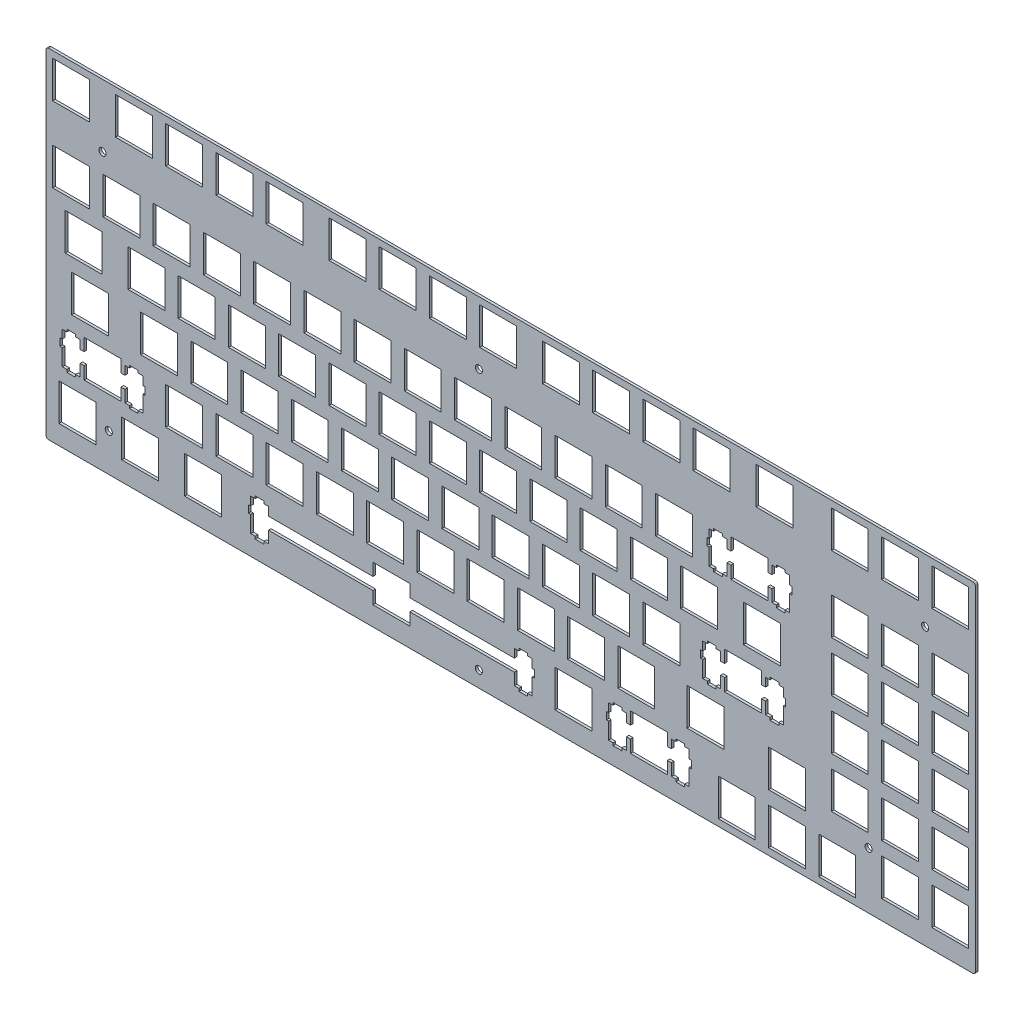
SolidWorks part; units mm, degrees
ref_plane "前视基准面" through (0, 0, 0) normal (0, 0, 1) x (1, 0, 0)
ref_plane "上视基准面" through (0, 0, 0) normal (0, 1, 0) x (1, 0, 0)
ref_plane "右视基准面" through (0, 0, 0) normal (1, 0, 0) x (0, 0, -1)
other "Configuration Table"
sketch "Model" plane through (0, 0, 0) normal (0, 0, 1) x (1, 0, 0)
  line L0 (0.0951, 129.021) -> (352.52, 129.021)
  line L1 (352.52, 129.021) -> (352.52, 0.4341)
  line L2 (352.52, 0.4341) -> (0.0951, 0.4341)
  line L3 (0.0951, 0.4341) -> (0.0951, 129.021)
  line L4 (255.032, 16.9595) -> (269.032, 16.9595)
  line L5 (269.032, 16.9595) -> (269.032, 2.96)
  line L6 (269.032, 2.96) -> (255.032, 2.96)
  line L7 (255.032, 2.96) -> (255.032, 16.9595)
  line L8 (274.082, 16.9595) -> (288.082, 16.9595)
  line L9 (288.082, 16.9595) -> (288.082, 2.96)
  line L10 (288.082, 2.96) -> (274.082, 2.96)
  line L11 (274.082, 2.96) -> (274.082, 16.9595)
  line L12 (293.132, 16.9595) -> (307.132, 16.9595)
  line L13 (307.132, 16.9595) -> (307.132, 2.96)
  line L14 (307.132, 2.96) -> (293.132, 2.96)
  line L15 (293.132, 2.96) -> (293.132, 16.9595)
  line L16 (124.062, 21.722) -> (124.062, 17.0215)
  line L17 (124.062, 17.0215) -> (84.4381, 17.0215)
  line L18 (84.4381, 17.0215) -> (84.4381, 20.2517)
  line L19 (84.4381, 20.2517) -> (82.7126, 20.2517)
  line L20 (82.7126, 20.2517) -> (82.7126, 21.1722)
  line L21 (82.7126, 21.1722) -> (79.412, 21.1722)
  line L22 (79.412, 21.1722) -> (79.412, 20.2517)
  line L23 (79.412, 20.2517) -> (77.687, 20.2517)
  line L24 (77.687, 20.2517) -> (77.687, 17.0215)
  line L25 (77.687, 17.0215) -> (76.8629, 17.0215)
  line L26 (76.8629, 17.0215) -> (76.8629, 14.2227)
  line L27 (76.8629, 14.2227) -> (77.687, 14.2227)
  line L28 (77.687, 14.2227) -> (77.687, 7.9527)
  line L29 (77.687, 7.9527) -> (79.412, 7.9527)
  line L30 (79.412, 7.9527) -> (79.412, 6.9715)
  line L31 (79.412, 6.9715) -> (82.7126, 6.9715)
  line L32 (82.7126, 6.9715) -> (82.7126, 7.9527)
  line L33 (82.7126, 7.9527) -> (84.4381, 7.9527)
  line L34 (84.4381, 7.9527) -> (84.4381, 12.4216)
  line L35 (84.4381, 12.4216) -> (124.062, 12.4216)
  line L36 (124.062, 12.4216) -> (124.062, 7.7225)
  line L37 (124.062, 7.7225) -> (138.063, 7.7225)
  line L38 (138.063, 7.7225) -> (138.063, 12.4216)
  line L39 (138.063, 12.4216) -> (177.687, 12.4216)
  line L40 (177.687, 12.4216) -> (177.687, 7.9527)
  line L41 (177.687, 7.9527) -> (179.412, 7.9527)
  line L42 (179.412, 7.9527) -> (179.412, 6.9715)
  line L43 (179.412, 6.9715) -> (182.713, 6.9715)
  line L44 (182.713, 6.9715) -> (182.713, 7.9527)
  line L45 (182.713, 7.9527) -> (184.438, 7.9527)
  line L46 (184.438, 7.9527) -> (184.438, 14.2227)
  line L47 (184.438, 14.2227) -> (185.262, 14.2227)
  line L48 (185.262, 14.2227) -> (185.262, 17.0215)
  line L49 (185.262, 17.0215) -> (184.438, 17.0215)
  line L50 (184.438, 17.0215) -> (184.438, 20.2517)
  line L51 (184.438, 20.2517) -> (182.713, 20.2517)
  line L52 (182.713, 20.2517) -> (182.713, 21.1722)
  line L53 (182.713, 21.1722) -> (179.412, 21.1722)
  line L54 (179.412, 21.1722) -> (179.412, 20.2517)
  line L55 (179.412, 20.2517) -> (177.687, 20.2517)
  line L56 (177.687, 20.2517) -> (177.687, 17.0215)
  line L57 (177.687, 17.0215) -> (138.063, 17.0215)
  line L58 (138.063, 17.0215) -> (138.063, 21.722)
  line L59 (138.063, 21.722) -> (124.062, 21.722)
  line L60 (221.695, 21.722) -> (221.695, 17.0215)
  line L61 (221.695, 17.0215) -> (220.169, 17.0215)
  line L62 (220.169, 17.0215) -> (220.169, 20.2517)
  line L63 (220.169, 20.2517) -> (218.444, 20.2517)
  line L64 (218.444, 20.2517) -> (218.444, 21.1722)
  line L65 (218.444, 21.1722) -> (215.145, 21.1722)
  line L66 (215.145, 21.1722) -> (215.145, 20.2517)
  line L67 (215.145, 20.2517) -> (213.42, 20.2517)
  line L68 (213.42, 20.2517) -> (213.42, 17.0215)
  line L69 (213.42, 17.0215) -> (212.594, 17.0215)
  line L70 (212.594, 17.0215) -> (212.594, 14.2227)
  line L71 (212.594, 14.2227) -> (213.42, 14.2227)
  line L72 (213.42, 14.2227) -> (213.42, 7.9527)
  line L73 (213.42, 7.9527) -> (215.145, 7.9527)
  line L74 (215.145, 7.9527) -> (215.145, 6.9715)
  line L75 (215.145, 6.9715) -> (218.444, 6.9715)
  line L76 (218.444, 6.9715) -> (218.444, 7.9527)
  line L77 (218.444, 7.9527) -> (220.169, 7.9527)
  line L78 (220.169, 7.9527) -> (220.169, 12.4216)
  line L79 (220.169, 12.4216) -> (221.695, 12.4216)
  line L80 (221.695, 12.4216) -> (221.695, 7.7225)
  line L81 (221.695, 7.7225) -> (235.694, 7.7225)
  line L82 (235.694, 7.7225) -> (235.694, 12.4216)
  line L83 (235.694, 12.4216) -> (237.22, 12.4216)
  line L84 (237.22, 12.4216) -> (237.22, 7.9527)
  line L85 (237.22, 7.9527) -> (238.945, 7.9527)
  line L86 (238.945, 7.9527) -> (238.945, 6.9715)
  line L87 (238.945, 6.9715) -> (242.244, 6.9715)
  line L88 (242.244, 6.9715) -> (242.244, 7.9527)
  line L89 (242.244, 7.9527) -> (243.969, 7.9527)
  line L90 (243.969, 7.9527) -> (243.969, 14.2227)
  line L91 (243.969, 14.2227) -> (244.795, 14.2227)
  line L92 (244.795, 14.2227) -> (244.795, 17.0215)
  line L93 (244.795, 17.0215) -> (243.969, 17.0215)
  line L94 (243.969, 17.0215) -> (243.969, 20.2517)
  line L95 (243.969, 20.2517) -> (242.244, 20.2517)
  line L96 (242.244, 20.2517) -> (242.244, 21.1722)
  line L97 (242.244, 21.1722) -> (238.945, 21.1722)
  line L98 (238.945, 21.1722) -> (238.945, 20.2517)
  line L99 (238.945, 20.2517) -> (237.22, 20.2517)
  line L100 (237.22, 20.2517) -> (237.22, 17.0215)
  line L101 (237.22, 17.0215) -> (235.694, 17.0215)
  line L102 (235.694, 17.0215) -> (235.694, 21.722)
  line L103 (235.694, 21.722) -> (221.695, 21.722)
  line L104 (5.0009, 21.722) -> (19.0004, 21.722)
  line L105 (19.0004, 21.722) -> (19.0004, 7.7225)
  line L106 (19.0004, 7.7225) -> (5.0009, 7.7225)
  line L107 (5.0009, 7.7225) -> (5.0009, 21.722)
  line L108 (28.812, 21.722) -> (42.8128, 21.722)
  line L109 (42.8128, 21.722) -> (42.8128, 7.7225)
  line L110 (42.8128, 7.7225) -> (28.812, 7.7225)
  line L111 (28.812, 7.7225) -> (28.812, 21.722)
  line L112 (52.626, 21.722) -> (66.6253, 21.722)
  line L113 (66.6253, 21.722) -> (66.6253, 7.7225)
  line L114 (66.6253, 7.7225) -> (52.626, 7.7225)
  line L115 (52.626, 7.7225) -> (52.626, 21.722)
  line L116 (193.12, 21.722) -> (207.119, 21.722)
  line L117 (207.119, 21.722) -> (207.119, 7.7225)
  line L118 (207.119, 7.7225) -> (193.12, 7.7225)
  line L119 (193.12, 7.7225) -> (193.12, 21.722)
  line L120 (316.945, 21.722) -> (330.944, 21.722)
  line L121 (330.944, 21.722) -> (330.944, 7.7225)
  line L122 (330.944, 7.7225) -> (316.945, 7.7225)
  line L123 (316.945, 7.7225) -> (316.945, 21.722)
  line L124 (335.995, 21.722) -> (349.994, 21.722)
  line L125 (349.994, 21.722) -> (349.994, 7.7225)
  line L126 (349.994, 7.7225) -> (335.995, 7.7225)
  line L127 (335.995, 7.7225) -> (335.995, 21.722)
  line L128 (274.082, 36.0094) -> (288.082, 36.0094)
  line L129 (288.082, 36.0094) -> (288.082, 22.01)
  line L130 (288.082, 22.01) -> (274.082, 22.01)
  line L131 (274.082, 22.01) -> (274.082, 36.0094)
  line L132 (14.5259, 40.7719) -> (14.5259, 36.0715)
  line L133 (14.5259, 36.0715) -> (13.0004, 36.0715)
  line L134 (13.0004, 36.0715) -> (13.0004, 39.3016)
  line L135 (13.0004, 39.3016) -> (11.2751, 39.3016)
  line L136 (11.2751, 39.3016) -> (11.2751, 40.2223)
  line L137 (11.2751, 40.2223) -> (7.9761, 40.2223)
  line L138 (7.9761, 40.2223) -> (7.9761, 39.3016)
  line L139 (7.9761, 39.3016) -> (6.2508, 39.3016)
  line L140 (6.2508, 39.3016) -> (6.2508, 36.0715)
  line L141 (6.2508, 36.0715) -> (5.4253, 36.0715)
  line L142 (5.4253, 36.0715) -> (5.4253, 33.2727)
  line L143 (5.4253, 33.2727) -> (6.2508, 33.2727)
  line L144 (6.2508, 33.2727) -> (6.2508, 27.0027)
  line L145 (6.2508, 27.0027) -> (7.9761, 27.0027)
  line L146 (7.9761, 27.0027) -> (7.9761, 26.0215)
  line L147 (7.9761, 26.0215) -> (11.2751, 26.0215)
  line L148 (11.2751, 26.0215) -> (11.2751, 27.0027)
  line L149 (11.2751, 27.0027) -> (13.0004, 27.0027)
  line L150 (13.0004, 27.0027) -> (13.0004, 31.4716)
  line L151 (13.0004, 31.4716) -> (14.5259, 31.4716)
  line L152 (14.5259, 31.4716) -> (14.5259, 26.7725)
  line L153 (14.5259, 26.7725) -> (28.5254, 26.7725)
  line L154 (28.5254, 26.7725) -> (28.5254, 31.4716)
  line L155 (28.5254, 31.4716) -> (30.0509, 31.4716)
  line L156 (30.0509, 31.4716) -> (30.0509, 27.0027)
  line L157 (30.0509, 27.0027) -> (31.7748, 27.0027)
  line L158 (31.7748, 27.0027) -> (31.7748, 26.0215)
  line L159 (31.7748, 26.0215) -> (35.0752, 26.0215)
  line L160 (35.0752, 26.0215) -> (35.0752, 27.0027)
  line L161 (35.0752, 27.0027) -> (36.8004, 27.0027)
  line L162 (36.8004, 27.0027) -> (36.8004, 33.2727)
  line L163 (36.8004, 33.2727) -> (37.6259, 33.2727)
  line L164 (37.6259, 33.2727) -> (37.6259, 36.0715)
  line L165 (37.6259, 36.0715) -> (36.8004, 36.0715)
  line L166 (36.8004, 36.0715) -> (36.8004, 39.3016)
  line L167 (36.8004, 39.3016) -> (35.0752, 39.3016)
  line L168 (35.0752, 39.3016) -> (35.0752, 40.2223)
  line L169 (35.0752, 40.2223) -> (31.7748, 40.2223)
  line L170 (31.7748, 40.2223) -> (31.7748, 39.3016)
  line L171 (31.7748, 39.3016) -> (30.0509, 39.3016)
  line L172 (30.0509, 39.3016) -> (30.0509, 36.0715)
  line L173 (30.0509, 36.0715) -> (28.5254, 36.0715)
  line L174 (28.5254, 36.0715) -> (28.5254, 40.7719)
  line L175 (28.5254, 40.7719) -> (14.5259, 40.7719)
  line L176 (45.4822, 40.7719) -> (59.4815, 40.7719)
  line L177 (59.4815, 40.7719) -> (59.4815, 26.7725)
  line L178 (59.4815, 26.7725) -> (45.4822, 26.7725)
  line L179 (45.4822, 26.7725) -> (45.4822, 40.7719)
  line L180 (64.5322, 40.7719) -> (78.5315, 40.7719)
  line L181 (78.5315, 40.7719) -> (78.5315, 26.7725)
  line L182 (78.5315, 26.7725) -> (64.5322, 26.7725)
  line L183 (64.5322, 26.7725) -> (64.5322, 40.7719)
  line L184 (83.5822, 40.7719) -> (97.5815, 40.7719)
  line L185 (97.5815, 40.7719) -> (97.5815, 26.7725)
  line L186 (97.5815, 26.7725) -> (83.5822, 26.7725)
  line L187 (83.5822, 26.7725) -> (83.5822, 40.7719)
  line L188 (102.632, 40.7719) -> (116.632, 40.7719)
  line L189 (116.632, 40.7719) -> (116.632, 26.7725)
  line L190 (116.632, 26.7725) -> (102.632, 26.7725)
  line L191 (102.632, 26.7725) -> (102.632, 40.7719)
  line L192 (121.682, 40.7719) -> (135.682, 40.7719)
  line L193 (135.682, 40.7719) -> (135.682, 26.7725)
  line L194 (135.682, 26.7725) -> (121.682, 26.7725)
  line L195 (121.682, 26.7725) -> (121.682, 40.7719)
  line L196 (140.732, 40.7719) -> (154.732, 40.7719)
  line L197 (154.732, 40.7719) -> (154.732, 26.7725)
  line L198 (154.732, 26.7725) -> (140.732, 26.7725)
  line L199 (140.732, 26.7725) -> (140.732, 40.7719)
  line L200 (159.782, 40.7719) -> (173.782, 40.7719)
  line L201 (173.782, 40.7719) -> (173.782, 26.7725)
  line L202 (173.782, 26.7725) -> (159.782, 26.7725)
  line L203 (159.782, 26.7725) -> (159.782, 40.7719)
  line L204 (178.832, 40.7719) -> (192.832, 40.7719)
  line L205 (192.832, 40.7719) -> (192.832, 26.7725)
  line L206 (192.832, 26.7725) -> (178.832, 26.7725)
  line L207 (178.832, 26.7725) -> (178.832, 40.7719)
  line L208 (197.882, 40.7719) -> (211.882, 40.7719)
  line L209 (211.882, 40.7719) -> (211.882, 26.7725)
  line L210 (211.882, 26.7725) -> (197.882, 26.7725)
  line L211 (197.882, 26.7725) -> (197.882, 40.7719)
  line L212 (216.932, 40.7719) -> (230.932, 40.7719)
  line L213 (230.932, 40.7719) -> (230.932, 26.7725)
  line L214 (230.932, 26.7725) -> (216.932, 26.7725)
  line L215 (216.932, 26.7725) -> (216.932, 40.7719)
  line L216 (243.126, 40.7719) -> (257.125, 40.7719)
  line L217 (257.125, 40.7719) -> (257.125, 26.7725)
  line L218 (257.125, 26.7725) -> (243.126, 26.7725)
  line L219 (243.126, 26.7725) -> (243.126, 40.7719)
  line L220 (297.895, 40.7719) -> (311.894, 40.7719)
  line L221 (311.894, 40.7719) -> (311.894, 26.7725)
  line L222 (311.894, 26.7725) -> (297.895, 26.7725)
  line L223 (297.895, 26.7725) -> (297.895, 40.7719)
  line L224 (316.945, 40.7719) -> (330.944, 40.7719)
  line L225 (330.944, 40.7719) -> (330.944, 26.7725)
  line L226 (330.944, 26.7725) -> (316.945, 26.7725)
  line L227 (316.945, 26.7725) -> (316.945, 40.7719)
  line L228 (335.995, 40.7719) -> (349.994, 40.7719)
  line L229 (349.994, 40.7719) -> (349.994, 26.7725)
  line L230 (349.994, 26.7725) -> (335.995, 26.7725)
  line L231 (335.995, 26.7725) -> (335.995, 40.7719)
  line L232 (257.412, 59.8219) -> (257.412, 55.1215)
  line L233 (257.412, 55.1215) -> (255.888, 55.1215)
  line L234 (255.888, 55.1215) -> (255.888, 58.3516)
  line L235 (255.888, 58.3516) -> (254.161, 58.3516)
  line L236 (254.161, 58.3516) -> (254.161, 59.2723)
  line L237 (254.161, 59.2723) -> (250.862, 59.2723)
  line L238 (250.862, 59.2723) -> (250.862, 58.3516)
  line L239 (250.862, 58.3516) -> (249.137, 58.3516)
  line L240 (249.137, 58.3516) -> (249.137, 55.1215)
  line L241 (249.137, 55.1215) -> (248.313, 55.1215)
  line L242 (248.313, 55.1215) -> (248.313, 52.3226)
  line L243 (248.313, 52.3226) -> (249.137, 52.3226)
  line L244 (249.137, 52.3226) -> (249.137, 46.0527)
  line L245 (249.137, 46.0527) -> (250.862, 46.0527)
  line L246 (250.862, 46.0527) -> (250.862, 45.0716)
  line L247 (250.862, 45.0716) -> (254.161, 45.0716)
  line L248 (254.161, 45.0716) -> (254.161, 46.0527)
  line L249 (254.161, 46.0527) -> (255.888, 46.0527)
  line L250 (255.888, 46.0527) -> (255.888, 50.5217)
  line L251 (255.888, 50.5217) -> (257.412, 50.5217)
  line L252 (257.412, 50.5217) -> (257.412, 45.8227)
  line L253 (257.412, 45.8227) -> (271.413, 45.8227)
  line L254 (271.413, 45.8227) -> (271.413, 50.5217)
  line L255 (271.413, 50.5217) -> (272.937, 50.5217)
  line L256 (272.937, 50.5217) -> (272.937, 46.0527)
  line L257 (272.937, 46.0527) -> (274.662, 46.0527)
  line L258 (274.662, 46.0527) -> (274.662, 45.0716)
  line L259 (274.662, 45.0716) -> (277.963, 45.0716)
  line L260 (277.963, 45.0716) -> (277.963, 46.0527)
  line L261 (277.963, 46.0527) -> (279.688, 46.0527)
  line L262 (279.688, 46.0527) -> (279.688, 52.3226)
  line L263 (279.688, 52.3226) -> (280.512, 52.3226)
  line L264 (280.512, 52.3226) -> (280.512, 55.1215)
  line L265 (280.512, 55.1215) -> (279.688, 55.1215)
  line L266 (279.688, 55.1215) -> (279.688, 58.3516)
  line L267 (279.688, 58.3516) -> (277.963, 58.3516)
  line L268 (277.963, 58.3516) -> (277.963, 59.2723)
  line L269 (277.963, 59.2723) -> (274.662, 59.2723)
  line L270 (274.662, 59.2723) -> (274.662, 58.3516)
  line L271 (274.662, 58.3516) -> (272.937, 58.3516)
  line L272 (272.937, 58.3516) -> (272.937, 55.1215)
  line L273 (272.937, 55.1215) -> (271.413, 55.1215)
  line L274 (271.413, 55.1215) -> (271.413, 59.8219)
  line L275 (271.413, 59.8219) -> (257.412, 59.8219)
  line L276 (9.762, 59.8219) -> (23.7629, 59.8219)
  line L277 (23.7629, 59.8219) -> (23.7629, 45.8227)
  line L278 (23.7629, 45.8227) -> (9.762, 45.8227)
  line L279 (9.762, 45.8227) -> (9.762, 59.8219)
  line L280 (35.9572, 59.8219) -> (49.9565, 59.8219)
  line L281 (49.9565, 59.8219) -> (49.9565, 45.8227)
  line L282 (49.9565, 45.8227) -> (35.9572, 45.8227)
  line L283 (35.9572, 45.8227) -> (35.9572, 59.8219)
  line L284 (55.0072, 59.8219) -> (69.0065, 59.8219)
  line L285 (69.0065, 59.8219) -> (69.0065, 45.8227)
  line L286 (69.0065, 45.8227) -> (55.0072, 45.8227)
  line L287 (55.0072, 45.8227) -> (55.0072, 59.8219)
  line L288 (74.0572, 59.8219) -> (88.0565, 59.8219)
  line L289 (88.0565, 59.8219) -> (88.0565, 45.8227)
  line L290 (88.0565, 45.8227) -> (74.0572, 45.8227)
  line L291 (74.0572, 45.8227) -> (74.0572, 59.8219)
  line L292 (93.1072, 59.8219) -> (107.107, 59.8219)
  line L293 (107.107, 59.8219) -> (107.107, 45.8227)
  line L294 (107.107, 45.8227) -> (93.1072, 45.8227)
  line L295 (93.1072, 45.8227) -> (93.1072, 59.8219)
  line L296 (112.157, 59.8219) -> (126.157, 59.8219)
  line L297 (126.157, 59.8219) -> (126.157, 45.8227)
  line L298 (126.157, 45.8227) -> (112.157, 45.8227)
  line L299 (112.157, 45.8227) -> (112.157, 59.8219)
  line L300 (131.207, 59.8219) -> (145.207, 59.8219)
  line L301 (145.207, 59.8219) -> (145.207, 45.8227)
  line L302 (145.207, 45.8227) -> (131.207, 45.8227)
  line L303 (131.207, 45.8227) -> (131.207, 59.8219)
  line L304 (150.257, 59.8219) -> (164.257, 59.8219)
  line L305 (164.257, 59.8219) -> (164.257, 45.8227)
  line L306 (164.257, 45.8227) -> (150.257, 45.8227)
  line L307 (150.257, 45.8227) -> (150.257, 59.8219)
  line L308 (169.307, 59.8219) -> (183.307, 59.8219)
  line L309 (183.307, 59.8219) -> (183.307, 45.8227)
  line L310 (183.307, 45.8227) -> (169.307, 45.8227)
  line L311 (169.307, 45.8227) -> (169.307, 59.8219)
  line L312 (188.357, 59.8219) -> (202.357, 59.8219)
  line L313 (202.357, 59.8219) -> (202.357, 45.8227)
  line L314 (202.357, 45.8227) -> (188.357, 45.8227)
  line L315 (188.357, 45.8227) -> (188.357, 59.8219)
  line L316 (207.407, 59.8219) -> (221.407, 59.8219)
  line L317 (221.407, 59.8219) -> (221.407, 45.8227)
  line L318 (221.407, 45.8227) -> (207.407, 45.8227)
  line L319 (207.407, 45.8227) -> (207.407, 59.8219)
  line L320 (226.457, 59.8219) -> (240.457, 59.8219)
  line L321 (240.457, 59.8219) -> (240.457, 45.8227)
  line L322 (240.457, 45.8227) -> (226.457, 45.8227)
  line L323 (226.457, 45.8227) -> (226.457, 59.8219)
  line L324 (297.895, 59.8219) -> (311.894, 59.8219)
  line L325 (311.894, 59.8219) -> (311.894, 45.8227)
  line L326 (311.894, 45.8227) -> (297.895, 45.8227)
  line L327 (297.895, 45.8227) -> (297.895, 59.8219)
  line L328 (316.945, 59.8219) -> (330.944, 59.8219)
  line L329 (330.944, 59.8219) -> (330.944, 45.8227)
  line L330 (330.944, 45.8227) -> (316.945, 45.8227)
  line L331 (316.945, 45.8227) -> (316.945, 59.8219)
  line L332 (335.995, 59.8219) -> (349.994, 59.8219)
  line L333 (349.994, 59.8219) -> (349.994, 45.8227)
  line L334 (349.994, 45.8227) -> (335.995, 45.8227)
  line L335 (335.995, 45.8227) -> (335.995, 59.8219)
  line L336 (7.3822, 78.8719) -> (21.3817, 78.8719)
  line L337 (21.3817, 78.8719) -> (21.3817, 64.8727)
  line L338 (21.3817, 64.8727) -> (7.3822, 64.8727)
  line L339 (7.3822, 64.8727) -> (7.3822, 78.8719)
  line L340 (31.1947, 78.8719) -> (45.194, 78.8719)
  line L341 (45.194, 78.8719) -> (45.194, 64.8727)
  line L342 (45.194, 64.8727) -> (31.1947, 64.8727)
  line L343 (31.1947, 64.8727) -> (31.1947, 78.8719)
  line L344 (50.2447, 78.8719) -> (64.244, 78.8719)
  line L345 (64.244, 78.8719) -> (64.244, 64.8727)
  line L346 (64.244, 64.8727) -> (50.2447, 64.8727)
  line L347 (50.2447, 64.8727) -> (50.2447, 78.8719)
  line L348 (69.2947, 78.8719) -> (83.294, 78.8719)
  line L349 (83.294, 78.8719) -> (83.294, 64.8727)
  line L350 (83.294, 64.8727) -> (69.2947, 64.8727)
  line L351 (69.2947, 64.8727) -> (69.2947, 78.8719)
  line L352 (88.3447, 78.8719) -> (102.344, 78.8719)
  line L353 (102.344, 78.8719) -> (102.344, 64.8727)
  line L354 (102.344, 64.8727) -> (88.3447, 64.8727)
  line L355 (88.3447, 64.8727) -> (88.3447, 78.8719)
  line L356 (107.395, 78.8719) -> (121.394, 78.8719)
  line L357 (121.394, 78.8719) -> (121.394, 64.8727)
  line L358 (121.394, 64.8727) -> (107.395, 64.8727)
  line L359 (107.395, 64.8727) -> (107.395, 78.8719)
  line L360 (126.445, 78.8719) -> (140.444, 78.8719)
  line L361 (140.444, 78.8719) -> (140.444, 64.8727)
  line L362 (140.444, 64.8727) -> (126.445, 64.8727)
  line L363 (126.445, 64.8727) -> (126.445, 78.8719)
  line L364 (145.495, 78.8719) -> (159.494, 78.8719)
  line L365 (159.494, 78.8719) -> (159.494, 64.8727)
  line L366 (159.494, 64.8727) -> (145.495, 64.8727)
  line L367 (145.495, 64.8727) -> (145.495, 78.8719)
  line L368 (164.545, 78.8719) -> (178.544, 78.8719)
  line L369 (178.544, 78.8719) -> (178.544, 64.8727)
  line L370 (178.544, 64.8727) -> (164.545, 64.8727)
  line L371 (164.545, 64.8727) -> (164.545, 78.8719)
  line L372 (183.595, 78.8719) -> (197.594, 78.8719)
  line L373 (197.594, 78.8719) -> (197.594, 64.8727)
  line L374 (197.594, 64.8727) -> (183.595, 64.8727)
  line L375 (183.595, 64.8727) -> (183.595, 78.8719)
  line L376 (202.645, 78.8719) -> (216.644, 78.8719)
  line L377 (216.644, 78.8719) -> (216.644, 64.8727)
  line L378 (216.644, 64.8727) -> (202.645, 64.8727)
  line L379 (202.645, 64.8727) -> (202.645, 78.8719)
  line L380 (221.695, 78.8719) -> (235.694, 78.8719)
  line L381 (235.694, 78.8719) -> (235.694, 64.8727)
  line L382 (235.694, 64.8727) -> (221.695, 64.8727)
  line L383 (221.695, 64.8727) -> (221.695, 78.8719)
  line L384 (240.745, 78.8719) -> (254.744, 78.8719)
  line L385 (254.744, 78.8719) -> (254.744, 64.8727)
  line L386 (254.744, 64.8727) -> (240.745, 64.8727)
  line L387 (240.745, 64.8727) -> (240.745, 78.8719)
  line L388 (264.557, 78.8719) -> (278.557, 78.8719)
  line L389 (278.557, 78.8719) -> (278.557, 64.8727)
  line L390 (278.557, 64.8727) -> (264.557, 64.8727)
  line L391 (264.557, 64.8727) -> (264.557, 78.8719)
  line L392 (297.895, 78.8719) -> (311.894, 78.8719)
  line L393 (311.894, 78.8719) -> (311.894, 64.8727)
  line L394 (311.894, 64.8727) -> (297.895, 64.8727)
  line L395 (297.895, 64.8727) -> (297.895, 78.8719)
  line L396 (316.945, 78.8719) -> (330.944, 78.8719)
  line L397 (330.944, 78.8719) -> (330.944, 64.8727)
  line L398 (330.944, 64.8727) -> (316.945, 64.8727)
  line L399 (316.945, 64.8727) -> (316.945, 78.8719)
  line L400 (335.995, 78.8719) -> (349.994, 78.8719)
  line L401 (349.994, 78.8719) -> (349.994, 64.8727)
  line L402 (349.994, 64.8727) -> (335.995, 64.8727)
  line L403 (335.995, 64.8727) -> (335.995, 78.8719)
  line L404 (259.795, 97.9219) -> (259.795, 93.2215)
  line L405 (259.795, 93.2215) -> (258.269, 93.2215)
  line L406 (258.269, 93.2215) -> (258.269, 96.4516)
  line L407 (258.269, 96.4516) -> (256.544, 96.4516)
  line L408 (256.544, 96.4516) -> (256.544, 97.3723)
  line L409 (256.544, 97.3723) -> (253.243, 97.3723)
  line L410 (253.243, 97.3723) -> (253.243, 96.4516)
  line L411 (253.243, 96.4516) -> (251.52, 96.4516)
  line L412 (251.52, 96.4516) -> (251.52, 93.2215)
  line L413 (251.52, 93.2215) -> (250.694, 93.2215)
  line L414 (250.694, 93.2215) -> (250.694, 90.4226)
  line L415 (250.694, 90.4226) -> (251.52, 90.4226)
  line L416 (251.52, 90.4226) -> (251.52, 84.1527)
  line L417 (251.52, 84.1527) -> (253.243, 84.1527)
  line L418 (253.243, 84.1527) -> (253.243, 83.1716)
  line L419 (253.243, 83.1716) -> (256.544, 83.1716)
  line L420 (256.544, 83.1716) -> (256.544, 84.1527)
  line L421 (256.544, 84.1527) -> (258.269, 84.1527)
  line L422 (258.269, 84.1527) -> (258.269, 88.6217)
  line L423 (258.269, 88.6217) -> (259.795, 88.6217)
  line L424 (259.795, 88.6217) -> (259.795, 83.9227)
  line L425 (259.795, 83.9227) -> (273.794, 83.9227)
  line L426 (273.794, 83.9227) -> (273.794, 88.6217)
  line L427 (273.794, 88.6217) -> (275.32, 88.6217)
  line L428 (275.32, 88.6217) -> (275.32, 84.1527)
  line L429 (275.32, 84.1527) -> (277.045, 84.1527)
  line L430 (277.045, 84.1527) -> (277.045, 83.1716)
  line L431 (277.045, 83.1716) -> (280.344, 83.1716)
  line L432 (280.344, 83.1716) -> (280.344, 84.1527)
  line L433 (280.344, 84.1527) -> (282.069, 84.1527)
  line L434 (282.069, 84.1527) -> (282.069, 90.4226)
  line L435 (282.069, 90.4226) -> (282.895, 90.4226)
  line L436 (282.895, 90.4226) -> (282.895, 93.2215)
  line L437 (282.895, 93.2215) -> (282.069, 93.2215)
  line L438 (282.069, 93.2215) -> (282.069, 96.4516)
  line L439 (282.069, 96.4516) -> (280.344, 96.4516)
  line L440 (280.344, 96.4516) -> (280.344, 97.3723)
  line L441 (280.344, 97.3723) -> (277.045, 97.3723)
  line L442 (277.045, 97.3723) -> (277.045, 96.4516)
  line L443 (277.045, 96.4516) -> (275.32, 96.4516)
  line L444 (275.32, 96.4516) -> (275.32, 93.2215)
  line L445 (275.32, 93.2215) -> (273.794, 93.2215)
  line L446 (273.794, 93.2215) -> (273.794, 97.9219)
  line L447 (273.794, 97.9219) -> (259.795, 97.9219)
  line L448 (2.6197, 97.9219) -> (16.6192, 97.9219)
  line L449 (16.6192, 97.9219) -> (16.6192, 83.9227)
  line L450 (16.6192, 83.9227) -> (2.6197, 83.9227)
  line L451 (2.6197, 83.9227) -> (2.6197, 97.9219)
  line L452 (21.6697, 97.9219) -> (35.669, 97.9219)
  line L453 (35.669, 97.9219) -> (35.669, 83.9227)
  line L454 (35.669, 83.9227) -> (21.6697, 83.9227)
  line L455 (21.6697, 83.9227) -> (21.6697, 97.9219)
  line L456 (40.7197, 97.9219) -> (54.719, 97.9219)
  line L457 (54.719, 97.9219) -> (54.719, 83.9227)
  line L458 (54.719, 83.9227) -> (40.7197, 83.9227)
  line L459 (40.7197, 83.9227) -> (40.7197, 97.9219)
  line L460 (59.7697, 97.9219) -> (73.769, 97.9219)
  line L461 (73.769, 97.9219) -> (73.769, 83.9227)
  line L462 (73.769, 83.9227) -> (59.7697, 83.9227)
  line L463 (59.7697, 83.9227) -> (59.7697, 97.9219)
  line L464 (78.8197, 97.9219) -> (92.819, 97.9219)
  line L465 (92.819, 97.9219) -> (92.819, 83.9227)
  line L466 (92.819, 83.9227) -> (78.8197, 83.9227)
  line L467 (78.8197, 83.9227) -> (78.8197, 97.9219)
  line L468 (97.8683, 97.9219) -> (111.869, 97.9219)
  line L469 (111.869, 97.9219) -> (111.869, 83.9227)
  line L470 (111.869, 83.9227) -> (97.8683, 83.9227)
  line L471 (97.8683, 83.9227) -> (97.8683, 97.9219)
  line L472 (116.918, 97.9219) -> (130.919, 97.9219)
  line L473 (130.919, 97.9219) -> (130.919, 83.9227)
  line L474 (130.919, 83.9227) -> (116.918, 83.9227)
  line L475 (116.918, 83.9227) -> (116.918, 97.9219)
  line L476 (135.97, 97.9219) -> (149.969, 97.9219)
  line L477 (149.969, 97.9219) -> (149.969, 83.9227)
  line L478 (149.969, 83.9227) -> (135.97, 83.9227)
  line L479 (135.97, 83.9227) -> (135.97, 97.9219)
  line L480 (155.02, 97.9219) -> (169.019, 97.9219)
  line L481 (169.019, 97.9219) -> (169.019, 83.9227)
  line L482 (169.019, 83.9227) -> (155.02, 83.9227)
  line L483 (155.02, 83.9227) -> (155.02, 97.9219)
  line L484 (174.07, 97.9219) -> (188.069, 97.9219)
  line L485 (188.069, 97.9219) -> (188.069, 83.9227)
  line L486 (188.069, 83.9227) -> (174.07, 83.9227)
  line L487 (174.07, 83.9227) -> (174.07, 97.9219)
  line L488 (193.12, 97.9219) -> (207.119, 97.9219)
  line L489 (207.119, 97.9219) -> (207.119, 83.9227)
  line L490 (207.119, 83.9227) -> (193.12, 83.9227)
  line L491 (193.12, 83.9227) -> (193.12, 97.9219)
  line L492 (212.17, 97.9219) -> (226.169, 97.9219)
  line L493 (226.169, 97.9219) -> (226.169, 83.9227)
  line L494 (226.169, 83.9227) -> (212.17, 83.9227)
  line L495 (212.17, 83.9227) -> (212.17, 97.9219)
  line L496 (231.22, 97.9219) -> (245.219, 97.9219)
  line L497 (245.219, 97.9219) -> (245.219, 83.9227)
  line L498 (245.219, 83.9227) -> (231.22, 83.9227)
  line L499 (231.22, 83.9227) -> (231.22, 97.9219)
  line L500 (297.895, 97.9219) -> (311.894, 97.9219)
  line L501 (311.894, 97.9219) -> (311.894, 83.9227)
  line L502 (311.894, 83.9227) -> (297.895, 83.9227)
  line L503 (297.895, 83.9227) -> (297.895, 97.9219)
  line L504 (316.945, 97.9219) -> (330.944, 97.9219)
  line L505 (330.944, 97.9219) -> (330.944, 83.9227)
  line L506 (330.944, 83.9227) -> (316.945, 83.9227)
  line L507 (316.945, 83.9227) -> (316.945, 97.9219)
  line L508 (335.995, 97.9219) -> (349.994, 97.9219)
  line L509 (349.994, 97.9219) -> (349.994, 83.9227)
  line L510 (349.994, 83.9227) -> (335.995, 83.9227)
  line L511 (335.995, 83.9227) -> (335.995, 97.9219)
  line L512 (2.6197, 126.497) -> (16.6192, 126.497)
  line L513 (16.6192, 126.497) -> (16.6192, 112.498)
  line L514 (16.6192, 112.498) -> (2.6197, 112.498)
  line L515 (2.6197, 112.498) -> (2.6197, 126.497)
  line L516 (26.4322, 126.497) -> (40.4315, 126.497)
  line L517 (40.4315, 126.497) -> (40.4315, 112.498)
  line L518 (40.4315, 112.498) -> (26.4322, 112.498)
  line L519 (26.4322, 112.498) -> (26.4322, 126.497)
  line L520 (45.4822, 126.497) -> (59.4815, 126.497)
  line L521 (59.4815, 126.497) -> (59.4815, 112.498)
  line L522 (59.4815, 112.498) -> (45.4822, 112.498)
  line L523 (45.4822, 112.498) -> (45.4822, 126.497)
  line L524 (64.5322, 126.497) -> (78.5315, 126.497)
  line L525 (78.5315, 126.497) -> (78.5315, 112.498)
  line L526 (78.5315, 112.498) -> (64.5322, 112.498)
  line L527 (64.5322, 112.498) -> (64.5322, 126.497)
  line L528 (83.5822, 126.497) -> (97.5815, 126.497)
  line L529 (97.5815, 126.497) -> (97.5815, 112.498)
  line L530 (97.5815, 112.498) -> (83.5822, 112.498)
  line L531 (83.5822, 112.498) -> (83.5822, 126.497)
  line L532 (107.395, 126.497) -> (121.394, 126.497)
  line L533 (121.394, 126.497) -> (121.394, 112.498)
  line L534 (121.394, 112.498) -> (107.395, 112.498)
  line L535 (107.395, 112.498) -> (107.395, 126.497)
  line L536 (126.445, 126.497) -> (140.444, 126.497)
  line L537 (140.444, 126.497) -> (140.444, 112.498)
  line L538 (140.444, 112.498) -> (126.445, 112.498)
  line L539 (126.445, 112.498) -> (126.445, 126.497)
  line L540 (145.495, 126.497) -> (159.494, 126.497)
  line L541 (159.494, 126.497) -> (159.494, 112.498)
  line L542 (159.494, 112.498) -> (145.495, 112.498)
  line L543 (145.495, 112.498) -> (145.495, 126.497)
  line L544 (164.545, 126.497) -> (178.544, 126.497)
  line L545 (178.544, 126.497) -> (178.544, 112.498)
  line L546 (178.544, 112.498) -> (164.545, 112.498)
  line L547 (164.545, 112.498) -> (164.545, 126.497)
  line L548 (188.357, 126.497) -> (202.357, 126.497)
  line L549 (202.357, 126.497) -> (202.357, 112.498)
  line L550 (202.357, 112.498) -> (188.357, 112.498)
  line L551 (188.357, 112.498) -> (188.357, 126.497)
  line L552 (207.407, 126.497) -> (221.407, 126.497)
  line L553 (221.407, 126.497) -> (221.407, 112.498)
  line L554 (221.407, 112.498) -> (207.407, 112.498)
  line L555 (207.407, 112.498) -> (207.407, 126.497)
  line L556 (226.457, 126.497) -> (240.457, 126.497)
  line L557 (240.457, 126.497) -> (240.457, 112.498)
  line L558 (240.457, 112.498) -> (226.457, 112.498)
  line L559 (226.457, 112.498) -> (226.457, 126.497)
  line L560 (245.507, 126.497) -> (259.507, 126.497)
  line L561 (259.507, 126.497) -> (259.507, 112.498)
  line L562 (259.507, 112.498) -> (245.507, 112.498)
  line L563 (245.507, 112.498) -> (245.507, 126.497)
  line L564 (269.32, 126.497) -> (283.319, 126.497)
  line L565 (283.319, 126.497) -> (283.319, 112.498)
  line L566 (283.319, 112.498) -> (269.32, 112.498)
  line L567 (269.32, 112.498) -> (269.32, 126.497)
  line L568 (297.895, 126.497) -> (311.894, 126.497)
  line L569 (311.894, 126.497) -> (311.894, 112.498)
  line L570 (311.894, 112.498) -> (297.895, 112.498)
  line L571 (297.895, 112.498) -> (297.895, 126.497)
  line L572 (316.945, 126.497) -> (330.944, 126.497)
  line L573 (330.944, 126.497) -> (330.944, 112.498)
  line L574 (330.944, 112.498) -> (316.945, 112.498)
  line L575 (316.945, 112.498) -> (316.945, 126.497)
  line L576 (335.995, 126.497) -> (349.994, 126.497)
  line L577 (349.994, 126.497) -> (349.994, 112.498)
  line L578 (349.994, 112.498) -> (335.995, 112.498)
  line L579 (335.995, 112.498) -> (335.995, 126.497)
extrude "凸台-拉伸1" add sketch "Model" along normal blind 1
fillet "圆角1" radius 1 4 edges at (0.0951, 129.021, 0.5) (352.52, 129.021, 0.5) (352.52, 0.4341, 0.5) (0.0951, 0.4341, 0.5)
sketch "草图2" plane through (0, 0, 1) normal (0, 0, 1) x (1, 0, 0)
  line L0 (307.132, 16.9595) -> (316.945, 26.7725) construction
  line L2 (16.6192, 97.9219) -> (26.4322, 112.498) construction
  line L3 (330.944, 97.9219) -> (335.995, 112.498) construction
  line L4 (159.494, 112.498) -> (169.019, 97.9219) construction
  line L5 (19.0004, 7.7225) -> (28.812, 21.722) construction
  line L6 (42.8128, 21.722) -> (28.812, 21.722) construction
  line L7 (28.812, 21.722) -> (28.812, 7.7225) construction
  line L8 (1.0951, 0.4341) -> (351.52, 0.4341) construction
  circle A1 centre (21.5257, 105.2099) radius 1.35
  circle A2 centre (23.9062, 14.7223) radius 1.35
  circle A5 centre (164.2565, 105.2099) radius 1.35
  circle A7 centre (312.0385, 21.866) radius 1.35
  circle A9 centre (333.4695, 105.2099) radius 1.35
  circle A10 centre (164.2565, 6.4341) radius 1.35
  dimension "D1" = 2.7
  dimension "D2" = 2.7
  dimension "D3" = 2.7
  dimension "D4" = 2.7
  dimension "D5" = 2.7
  dimension "D7" = 2.7
  dimension "D6" = 6
extrude "切除-拉伸1" cut sketch "草图2" against normal blind 1.5
